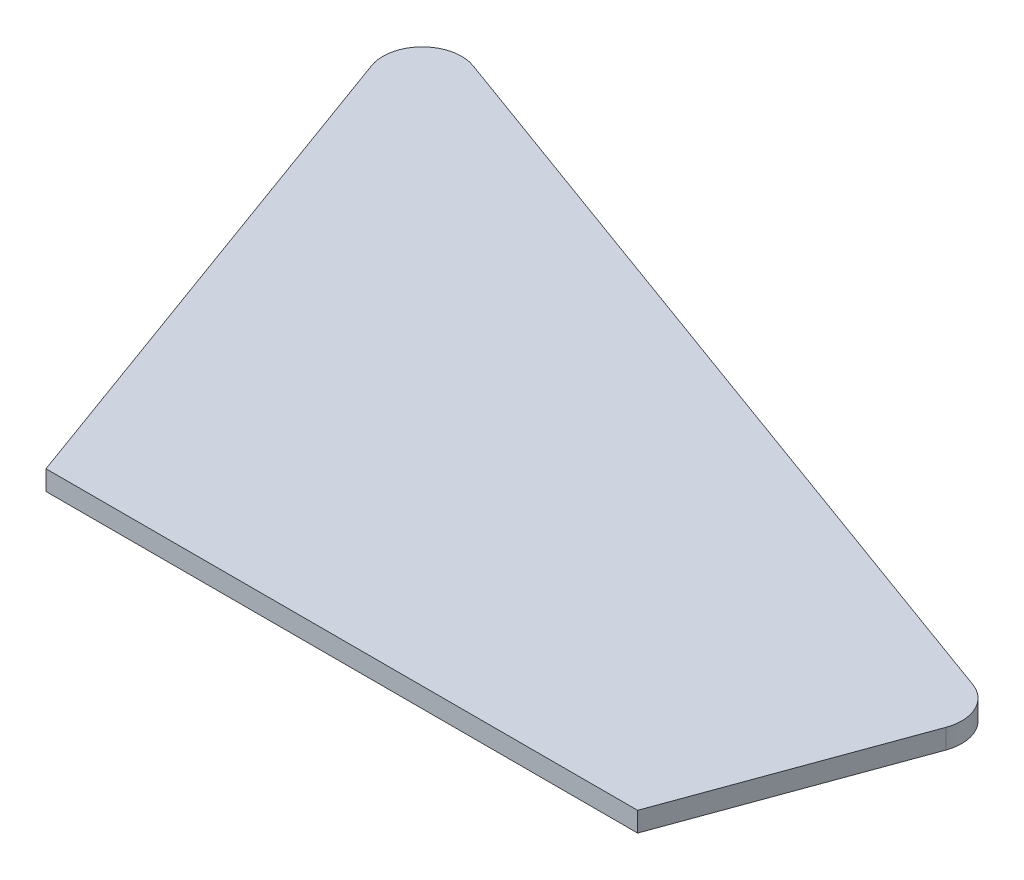
SolidWorks part; units mm, degrees
ref_plane "Front Plane" through (0, 0, 0) normal (0, 0, 1) x (1, 0, 0)
ref_plane "Top Plane" through (0, 0, 0) normal (0, 1, 0) x (1, 0, 0)
ref_plane "Right Plane" through (0, 0, 0) normal (1, 0, 0) x (0, 0, -1)
sketch "Sketch1" plane through (0, 0, 0) normal (0, 1, 0) x (1, 0, 0)
  line L0 (-24.719, -28.6537) -> (35.281, -28.6537)
  line L1 (35.281, -28.6537) -> (43.6233, -5.7334)
  line L2 (-24.719, -28.6537) -> (-43.6233, 23.2856)
  line L3 (1.3681, 13.9029) -> (41.2326, -0.6066)
  line L4 (1.3681, 13.9029) -> (-38.4965, 28.4125)
  arc A0 (41.2326, -0.6066) -> (43.6233, -5.7334) centre (39.8646, -4.3653) cw
  arc A1 (-38.4965, 28.4125) -> (-43.6233, 23.2856) centre (-39.8646, 24.6537) ccw
extrude "Boss-Extrude1" add sketch "Sketch1" along normal blind 2
sketch "Sketch3" plane through (0, 0, 0) normal (0, -1, 0) x (1, 0, 0)
  line L8 (-22.2682, 25.1537) -> (-40.3344, -24.4827)
  line L9 (-39.6935, -25.1235) -> (40.0356, 3.8955)
  line L10 (40.3344, 4.5363) -> (32.8303, 25.1537)
  line L11 (32.8303, 25.1537) -> (-22.2682, 25.1537)
  line L12 (-22.2682, 25.1537) -> (-40.3344, -24.4827)
  line L13 (-39.6935, -25.1235) -> (40.0356, 3.8955)
  line L14 (40.3344, 4.5363) -> (32.8303, 25.1537)
  line L15 (32.8303, 25.1537) -> (-22.2682, 25.1537)
  arc A4 (-40.3344, -24.4827) -> (-39.6935, -25.1235) centre (-39.8646, -24.6537) ccw
  arc A5 (40.0356, 3.8955) -> (40.3344, 4.5363) centre (39.8646, 4.3653) ccw
  arc A6 (-40.3344, -24.4827) -> (-39.6935, -25.1235) centre (-39.8646, -24.6537) ccw
  arc A7 (40.0356, 3.8955) -> (40.3344, 4.5363) centre (39.8646, 4.3653) ccw
  dimension "D1" = 3.5
extrude "Boss-Extrude2" add sketch "Sketch3" along normal blind 2
